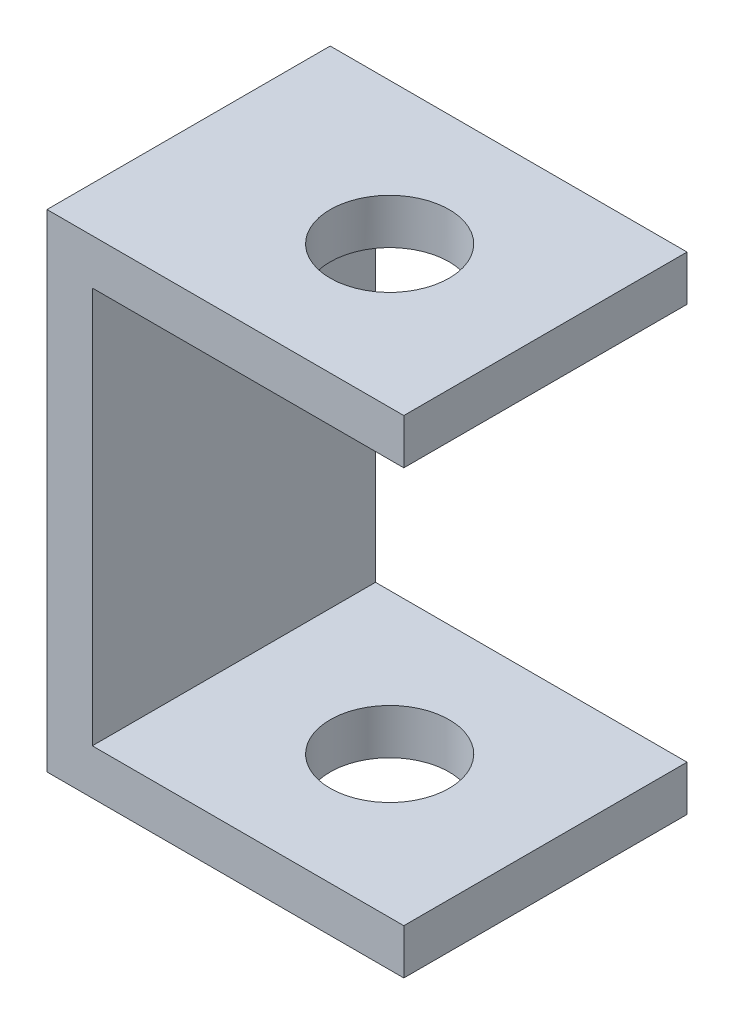
SolidWorks part; units mm, degrees
ref_plane "Płaszczyzna przednia" through (0, 0, 0) normal (0, 0, 1) x (1, 0, 0)
ref_plane "Płaszczyzna górna" through (0, 0, 0) normal (0, 1, 0) x (1, 0, 0)
ref_plane "Płaszczyzna prawa" through (0, 0, 0) normal (1, 0, 0) x (0, 0, -1)
sketch "Szkic1" plane through (0, 0, 0) normal (0, 0, 1) x (1, 0, 0)
  line L0 (0, 0) -> (-63, 0)
  line L1 (-63, 0) -> (-63, 86)
  line L2 (-63, 86) -> (0, 86)
  line L3 (0, 86) -> (0, 78)
  line L4 (0, 78) -> (-55, 78)
  line L5 (-55, 78) -> (-55, 8)
  line L6 (-55, 8) -> (0, 8)
  line L7 (0, 8) -> (0, 0)
  dimension "D1" = 70
  dimension "D2" = 8
  dimension "D3" = 8
  dimension "D4" = 8
  dimension "D5" = 55
extrude "Dodanie-wyciągnięcie1" add sketch "Szkic1" along normal blind 50 contours L4 L5 L6 L7 L0 L1 L2 L3
sketch "Szkic2" plane through (0, 86, 0) normal (0, 1, 0) x (1, 0, 0)
  line L0 (-63, -50) -> (0, -50) construction
  line L1 (0, 0) -> (-55, 0) construction
  line L2 (0, 0) -> (0, -50) construction
  line L3 (0, -50) -> (-55, -50) construction
  line L4 (-55, 0) -> (-55, -50) construction
  line L5 (-55, -50) -> (0, 0) construction
  line L6 (-55, 0) -> (0, -50) construction
  circle A0 centre (-27.5, -25) radius 10.5
  dimension "D2" = 21
  dimension "D1" = 55
extrude "Wytnij-wyciągnięcie1" cut sketch "Szkic2" against normal through all
